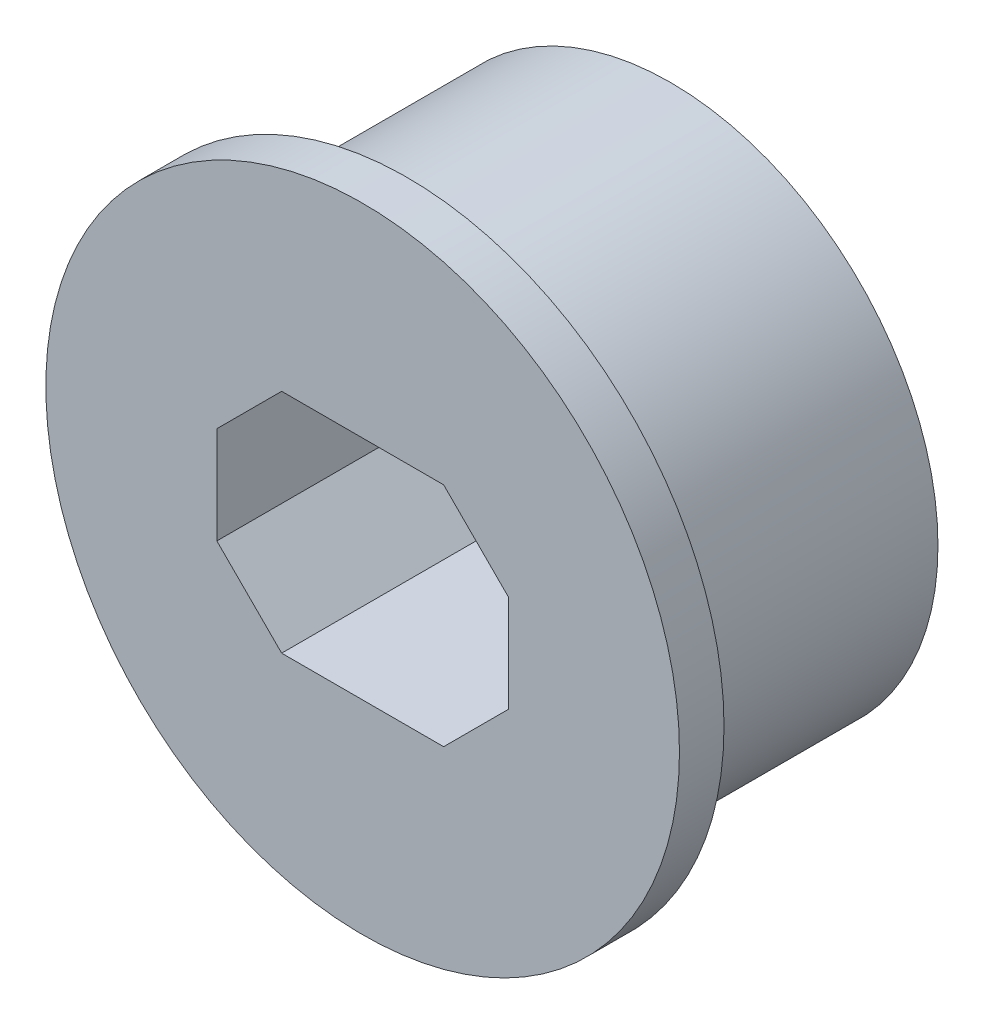
SolidWorks part; units mm, degrees
material "Nylon 101"
ref_plane "Front Plane" through (0, 0, 0) normal (0, 0, 1) x (1, 0, 0)
ref_plane "Top Plane" through (0, 0, 0) normal (0, 1, 0) x (1, 0, 0)
ref_plane "Right Plane" through (0, 0, 0) normal (1, 0, 0) x (0, 0, -1)
sketch "Sketch1" plane through (0, 0, 0) normal (0, 0, 1) x (1, 0, 0)
  circle A0 centre (6.731, -165.7192) radius 4.1275
  dimension "D1" = 8.255
extrude "Boss-Extrude2" add sketch "Sketch1" against normal blind 4.064
sketch "Sketch2" plane through (0, 0, 0) normal (0, 0, 1) x (1, 0, 0)
  circle A2 centre (6.731, -165.7192) radius 4.8895
  circle A3 centre (6.731, -165.7192) radius 4.8895
  dimension "D1" = 0.762
extrude "Boss-Extrude3" add sketch "Sketch2" along normal blind 1.5875
sketch "Sketch3" plane through (0, 0, 1.5875) normal (0, 0, 1) x (1, 0, 0)
  circle A0 centre (6.731, -165.7192) radius 0.635
  dimension "D1" = 1.27
split line "Split Line1" [suppressed]
dome "Dome1" [suppressed] faces to dome 1 distance 0.635 parameters "D1"=0.635
hole_wizard "#56 (0.0465) Diameter Hole1" [suppressed] positions "Sketch5" profile "Sketch4" hole size "#56" standard "ANSI Inch"
sketch "Sketch5" plane through (0, 0, -4.064) normal (0, 0, -1) x (-1, 0, 0)
  point P0 (-6.731, -165.7192)
sketch "Sketch4" plane through (6.731, -165.7192, -4.064) normal (1, 0, 0) x (0, 1, 0)
  line L0 (0, 0) -> (0, 5.6515)
  line L1 (0, 5.6515) -> (0.5905, 5.6515)
  line L2 (0.5905, 5.6515) -> (0.5905, 0)
  line L5 (0.5905, 0) -> (0, 0)
  line L11 (0, -6.35) -> (0, 107.95) construction
  dimension "Thru Hole Dia." = 1.1811
  dimension "Thru Hole Depth" = 5.6515
sketch "Sketch6" [suppressed] plane through (0, 0, -4.064) normal (0, 0, -1) x (-1, 0, 0)
  circle A0 centre (-6.731, -165.7192) radius 2.25
  dimension "D1" = 4.5
extrude "Cut-Extrude1" [suppressed] cut sketch "Sketch6" against normal through all
sketch "Sketch7" plane through (0, 0, -4.064) normal (0, 0, -1) x (-1, 0, 0)
  line L1 (-8.981, -163.9692) -> (-4.481, -163.9692)
  line L2 (-8.981, -163.9692) -> (-8.981, -167.4692)
  line L3 (-8.981, -167.4692) -> (-4.481, -167.4692)
  line L4 (-4.481, -163.9692) -> (-4.481, -167.4692)
  line L5 (-8.981, -163.9692) -> (-4.481, -167.4692) construction
  line L6 (-8.981, -167.4692) -> (-4.481, -163.9692) construction
  point P0 (-6.731, -165.7192)
  dimension "D1" = 4.5
  dimension "D2" = 3.5
extrude "Cut-Extrude2" cut sketch "Sketch7" against normal through all
chamfer "Chamfer1" distance 1 angle 45 4 edges at (8.981, -163.9692, -1.2383) (8.981, -167.4692, -1.2382) (4.481, -167.4692, -1.2382) (4.481, -163.9692, -1.2382)
sketch "Sketch8" plane through (0, 0, 1.5875) normal (0, 0, 1) x (1, 0, 0)
  circle A0 centre (6.731, -165.7192) radius 4.8895 construction
  circle A1 centre (6.731, -165.7192) radius 4.8895
extrude "Cut-Extrude3" cut sketch "Sketch8" against normal blind 0.9
